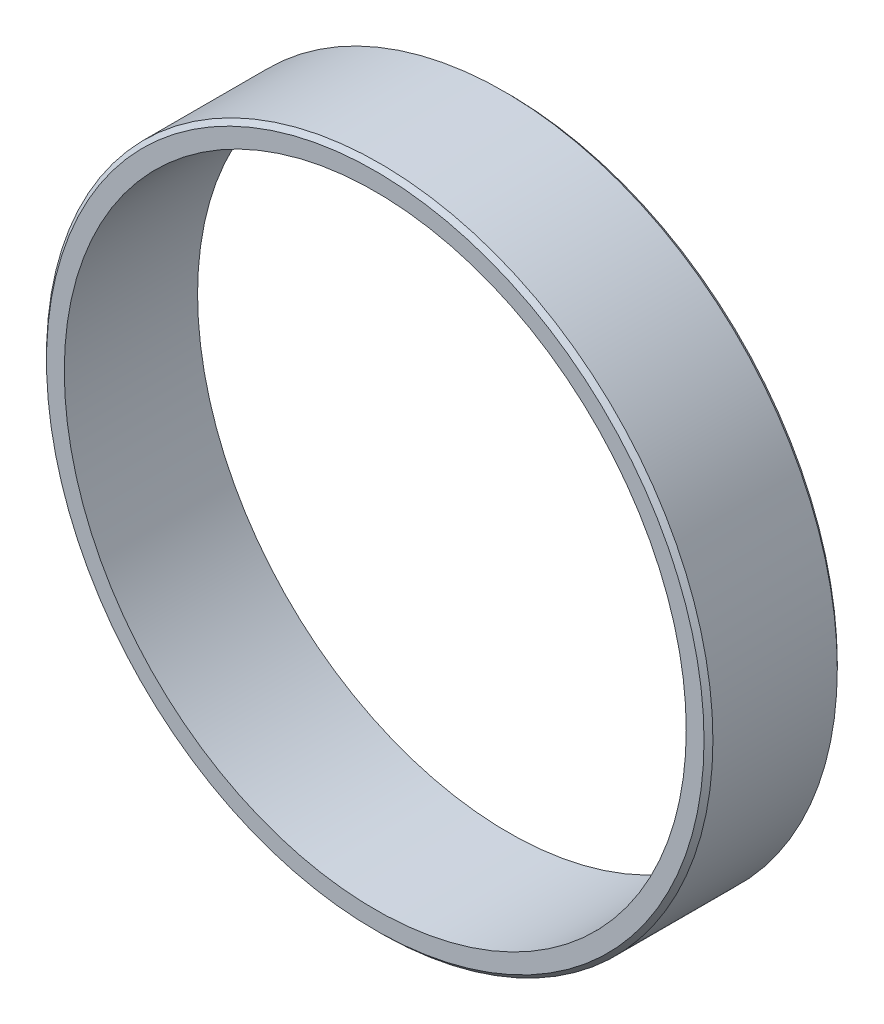
SolidWorks part; units mm, degrees
ref_plane "Front Plane" through (0, 0, 0) normal (0, 0, 1) x (1, 0, 0)
ref_plane "Top Plane" through (0, 0, 0) normal (0, 1, 0) x (1, 0, 0)
ref_plane "Right Plane" through (0, 0, 0) normal (1, 0, 0) x (0, 0, -1)
sketch "Sketch1" plane through (0, 0, 0) normal (0, 0, 1) x (1, 0, 0)
  circle A0 centre (0, 0) radius 37.5
  circle A1 centre (0, 0) radius 35
  dimension "D1" = 75
  dimension "D2" = 70
extrude "Boss-Extrude1" add sketch "Sketch1" along normal mid plane 15
chamfer "Chamfer1" distance 0.5 angle 45 2 edges at (37.5, 0, -7.5) (37.5, 0, 7.5)
